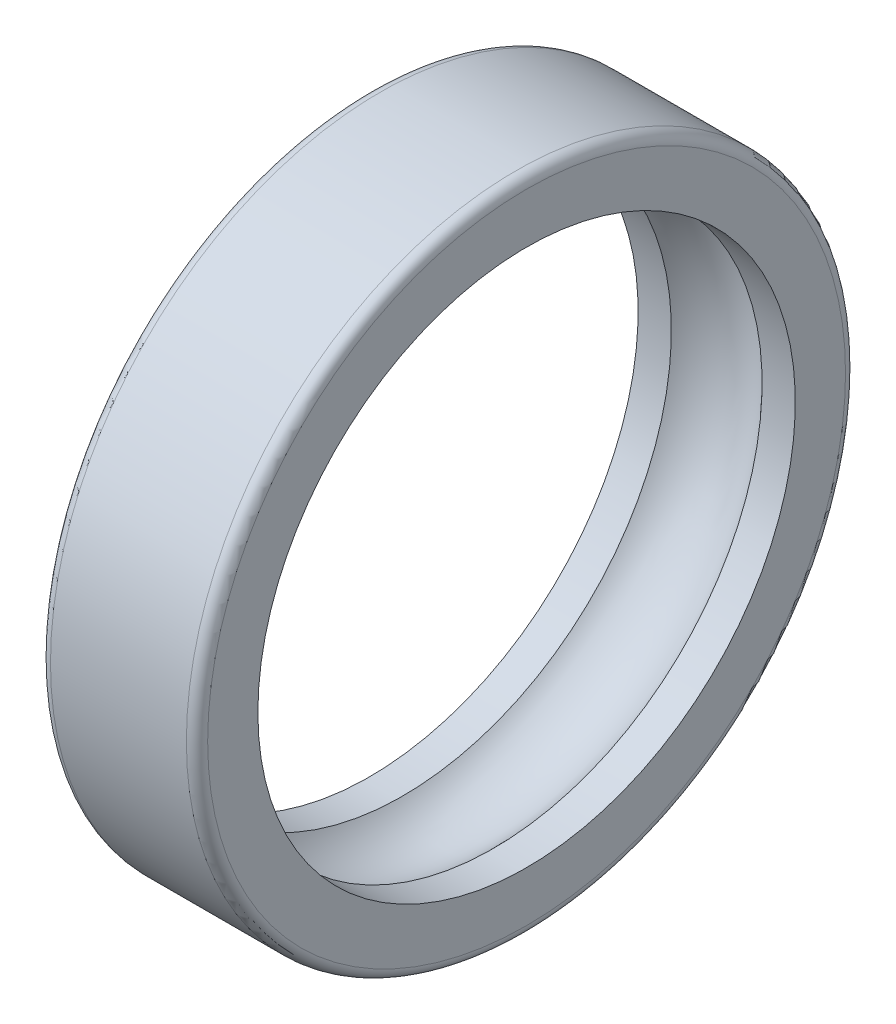
SolidWorks part; units mm, degrees
ref_plane "Front Plane" through (0, 0, 0) normal (0, 0, 1) x (1, 0, 0)
ref_plane "Top Plane" through (0, 0, 0) normal (0, 1, 0) x (1, 0, 0)
ref_plane "Right Plane" through (0, 0, 0) normal (1, 0, 0) x (0, 0, -1)
sketch "Sketch1" plane through (0, 0, 0) normal (0, 0, 1) x (1, 0, 0)
  line L0 (-47.7917, 0) -> (59.6319, 0) construction
  line L1 (0, 59) -> (0, -2.5265) construction
  line L2 (-15.5, 53) -> (-8.9443, 53)
  line L3 (-15.5, 53) -> (-15.5, 65)
  line L4 (-15.5, 65) -> (15.5, 65)
  line L5 (15.5, 53) -> (15.5, 65)
  line L6 (-15.5, 53) -> (15.5, 65) construction
  line L7 (-15.5, 65) -> (15.5, 53) construction
  line L8 (8.9443, 53) -> (15.5, 53)
  arc A0 (-8.9443, 53) -> (8.9443, 53) centre (0, 45) cw
  point P3 (0, 59)
  dimension "D5" = 12
  dimension "D1" = 31
  dimension "D2" = 65
  dimension "D3" = 53
  dimension "D4" = 8
revolve "Revolve1" add sketch "Sketch1" angle 360 about L0
fillet "Fillet1" radius 2.1 2 edges at (15.5, 0, 65) (-15.5, 0, 65)
